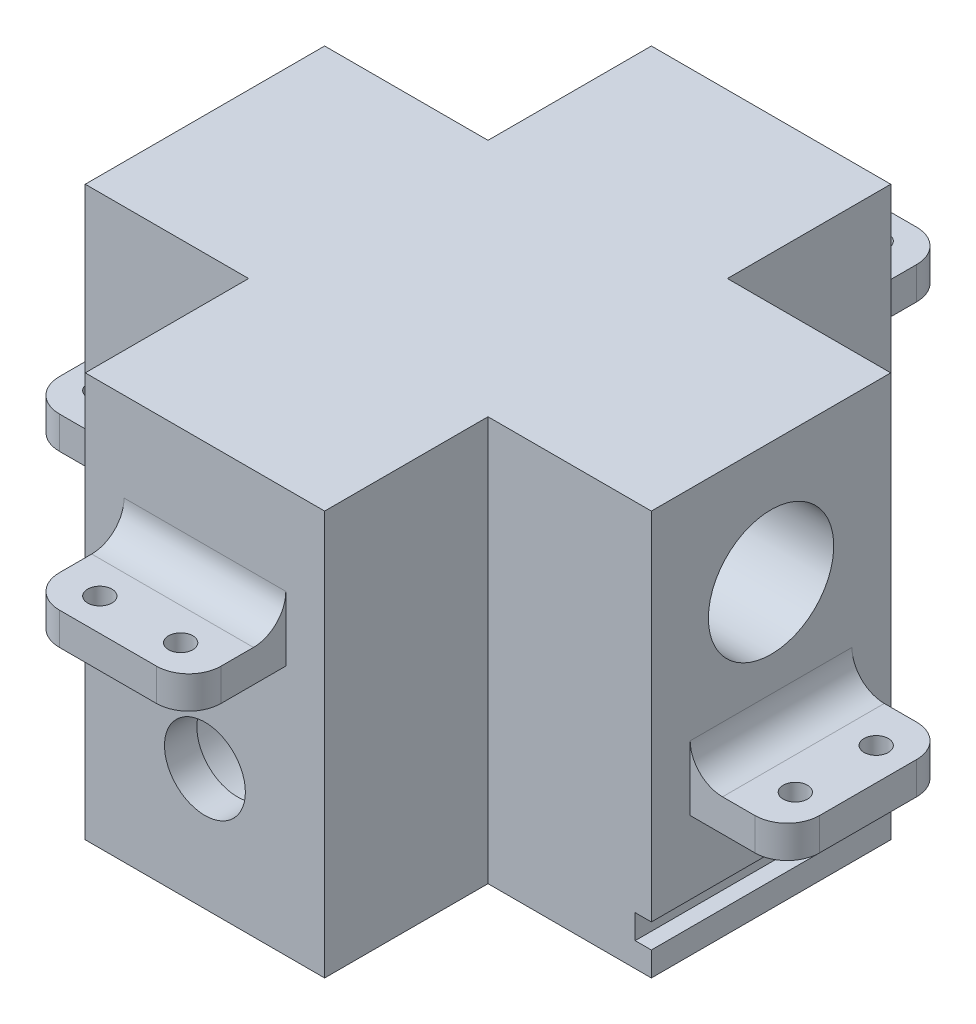
SolidWorks part; units mm, degrees
ref_plane "Plan de face" through (0, 0, 0) normal (0, 0, 1) x (1, 0, 0)
ref_plane "Plan de dessus" through (0, 0, 0) normal (0, 1, 0) x (1, 0, 0)
ref_plane "Plan de droite" through (0, 0, 0) normal (1, 0, 0) x (0, 0, -1)
sketch "Esquisse1" plane through (0, 0, 0) normal (1, 0, 0) x (0, 0, -1)
  line L2 (0, 0) -> (70, 0)
  line L3 (0, 0) -> (0, 50)
  line L4 (0, 50) -> (70, 50)
  line L5 (70, 0) -> (70, 50)
  dimension "D1" = 50
  dimension "D2" = 70
extrude "Boss.-Extru.1" add sketch "Esquisse1" along normal blind 70
sketch "Esquisse2" plane through (0, 0, 0) normal (0, 0, 1) x (1, 0, 0)
  line L0 (70, 0) -> (0, 0) construction
  line L1 (0, 50) -> (0, 0) construction
  circle A0 centre (35, 15) radius 7.75
  dimension "D1" = 15.5
  dimension "D2" = 15
  dimension "D3" = 35
extrude "Enlèv. mat.-Extru.1" cut sketch "Esquisse2" against normal through all
sketch "Esquisse3" plane through (0, 0, 0) normal (-1, 0, 0) x (0, 0, 1)
  line L0 (-70, 50) -> (0, 50) construction
  line L1 (0, 50) -> (0, 0) construction
  circle A0 centre (-35, 35) radius 7.75
  dimension "D1" = 15.5
  dimension "D2" = 15
  dimension "D3" = 35
extrude "Enlèv. mat.-Extru.2" cut sketch "Esquisse3" against normal through all
sketch "Esquisse4" plane through (0, 0, 0) normal (0, -1, 0) x (1, 0, 0)
  line L1 (0, -70) -> (20.2, -70)
  line L2 (0, -70) -> (0, -49.8)
  line L3 (0, -49.8) -> (20.2, -49.8)
  line L4 (20.2, -70) -> (20.2, -49.8)
  line L5 (0, 0) -> (20.2, 0)
  line L6 (0, 0) -> (0, -20.2)
  line L7 (0, -20.2) -> (20.2, -20.2)
  line L8 (20.2, 0) -> (20.2, -20.2)
  line L9 (70, 0) -> (49.8, 0)
  line L10 (70, 0) -> (70, -20.2)
  line L11 (70, -20.2) -> (49.8, -20.2)
  line L12 (49.8, 0) -> (49.8, -20.2)
  line L13 (70, -70) -> (49.8, -70)
  line L14 (70, -70) -> (70, -49.8)
  line L15 (70, -49.8) -> (49.8, -49.8)
  line L16 (49.8, -70) -> (49.8, -49.8)
  dimension "D1" = 20.2
  dimension "D2" = 20.2
  dimension "D3" = 20.2
  dimension "D4" = 20.2
  dimension "D5" = 20.2
  dimension "D6" = 20.2
  dimension "D7" = 20.2
  dimension "D8" = 20.2
extrude "Enlèv. mat.-Extru.3" cut sketch "Esquisse4" against normal through all
sketch "Esquisse7" plane through (0, 0, 0) normal (0, 0, 1) x (1, 0, 0)
  circle A0 centre (35, 15) radius 5
  circle A1 centre (35, 15) radius 11.7367
  dimension "D1" = 10
extrude "Boss.-Extru.3" add sketch "Esquisse7" against normal blind 4
sketch "Esquisse8" plane through (0, 0, 0) normal (-1, 0, 0) x (0, 0, 1)
  circle A0 centre (-35, 35) radius 12.1967
  circle A1 centre (-35, 35) radius 5
  dimension "D1" = 10
extrude "Boss.-Extru.4" add sketch "Esquisse8" against normal blind 4
sketch "Esquisse9" plane through (20.2, 0, 0) normal (-1, 0, 0) x (0, 0, 1)
  line L0 (-70, 50) -> (-70, 0) construction
  line L1 (-70, 6) -> (-68, 6)
  line L2 (-70, 6) -> (-70, 3)
  line L3 (-70, 3) -> (-68, 3)
  line L4 (-68, 6) -> (-68, 3)
  line L5 (-70, 0) -> (-49.8, 0) construction
  dimension "D1" = 3
  dimension "D2" = 3
  dimension "D3" = 2
extrude "Enlèv. mat.-Extru.4" cut sketch "Esquisse9" against normal through all
sketch "Esquisse10" plane through (0, 0, -49.8) normal (0, 0, -1) x (-1, 0, 0)
  line L0 (0, 50) -> (0, 0) construction
  line L1 (0, 3) -> (-2, 3)
  line L2 (0, 3) -> (0, 6)
  line L3 (0, 6) -> (-2, 6)
  line L4 (-2, 3) -> (-2, 6)
  line L5 (-20.2, 0) -> (0, 0) construction
  dimension "D1" = 3
  dimension "D2" = 2
  dimension "D3" = 3
extrude "Enlèv. mat.-Extru.5" cut sketch "Esquisse10" against normal through all
sketch "Esquisse11" plane through (0, 0, -49.8) normal (0, 0, -1) x (-1, 0, 0)
  line L0 (-70, 50) -> (-70, 0) construction
  line L1 (-70, 6) -> (-68, 6)
  line L2 (-70, 6) -> (-70, 3)
  line L3 (-70, 3) -> (-68, 3)
  line L4 (-68, 6) -> (-68, 3)
  line L5 (-70, 0) -> (-49.8, 0) construction
  dimension "D1" = 3
  dimension "D2" = 3
  dimension "D3" = 2
extrude "Enlèv. mat.-Extru.6" cut sketch "Esquisse11" against normal through all
sketch "Esquisse12" plane through (0, 0, 0) normal (-1, 0, 0) x (0, 0, 1)
  line L0 (-49.8, 50) -> (-49.8, 6) construction
  line L1 (-25, 15) -> (-45, 15)
  line L2 (-25, 15) -> (-25, 19)
  line L3 (-25, 19) -> (-45, 19)
  line L4 (-45, 15) -> (-45, 19)
  line L5 (-20.2, 50) -> (-20.2, 6) construction
  line L6 (-20.2, 0) -> (-49.8, 0) construction
  dimension "D1" = 4
  dimension "D2" = 20
  dimension "D3" = 4.8
  dimension "D4" = 4.8
  dimension "D5" = 15
extrude "Boss.-Extru.5" add sketch "Esquisse12" along normal blind 12
sketch "Esquisse13" plane through (0, 15, 0) normal (0, -1, 0) x (1, 0, 0)
  line L0 (0, -45) -> (0, -25) construction
  line L1 (-12, -45) -> (0, -45) construction
  line L2 (-12, -25) -> (0, -25) construction
  circle A0 centre (-8, -30) radius 1.5
  circle A1 centre (-8, -40) radius 1.5
  dimension "D1" = 3
  dimension "D2" = 3
  dimension "D3" = 8
  dimension "D4" = 8
  dimension "D5" = 10
  dimension "D6" = 5
  dimension "D7" = 5
extrude "Enlèv. mat.-Extru.7" cut sketch "Esquisse13" against normal through all
fillet "Congé1" radius 4 2 edges at (-12, 17, -25) (-12, 17, -45)
sketch "Esquisse14" plane through (70, 0, 0) normal (1, 0, 0) x (0, 0, -1)
  line L0 (49.8, 50) -> (49.8, 6) construction
  line L1 (45, 15) -> (25, 15)
  line L2 (45, 15) -> (45, 19)
  line L3 (45, 19) -> (25, 19)
  line L4 (25, 15) -> (25, 19)
  line L5 (20.2, 50) -> (20.2, 6) construction
  line L6 (20.2, 0) -> (49.8, 0) construction
  dimension "D1" = 4
  dimension "D2" = 20
  dimension "D3" = 4.8
  dimension "D4" = 4.8
  dimension "D5" = 15
extrude "Boss.-Extru.6" add sketch "Esquisse14" along normal blind 12
sketch "Esquisse15" plane through (0, 15, 0) normal (0, -1, 0) x (1, 0, 0)
  line L0 (82, -45) -> (70, -45) construction
  line L1 (70, -25) -> (70, -45) construction
  line L2 (82, -25) -> (70, -25) construction
  circle A0 centre (78, -40) radius 1.5
  circle A1 centre (78, -30) radius 1.5
  dimension "D1" = 3
  dimension "D2" = 3
  dimension "D3" = 10
  dimension "D4" = 5
  dimension "D5" = 8
  dimension "D6" = 5
extrude "Enlèv. mat.-Extru.8" cut sketch "Esquisse15" against normal through all
fillet "Congé3" radius 4 2 edges at (82, 17, -45) (82, 17, -25)
sketch "Esquisse16" plane through (0, 0, 0) normal (0, 0, 1) x (1, 0, 0)
  line L0 (49.8, 50) -> (20.2, 50) construction
  line L1 (45, 31) -> (25, 31)
  line L2 (45, 31) -> (45, 35)
  line L3 (45, 35) -> (25, 35)
  line L4 (25, 31) -> (25, 35)
  line L5 (20.2, 50) -> (20.2, 0) construction
  line L6 (49.8, 50) -> (49.8, 0) construction
  dimension "D1" = 20
  dimension "D2" = 4
  dimension "D3" = 15
  dimension "D4" = 4.8
  dimension "D5" = 4.8
extrude "Boss.-Extru.7" add sketch "Esquisse16" along normal blind 12
sketch "Esquisse17" plane through (0, 31, 0) normal (0, -1, 0) x (1, 0, 0)
  line L0 (25, 0) -> (45, 0) construction
  line L1 (25, 12) -> (25, 0) construction
  circle A0 centre (40, 8) radius 1.5
  circle A1 centre (30, 8) radius 1.5
  dimension "D1" = 3
  dimension "D2" = 3
  dimension "D3" = 10
  dimension "D4" = 8
  dimension "D5" = 8
  dimension "D6" = 5
extrude "Enlèv. mat.-Extru.9" cut sketch "Esquisse17" against normal through all
fillet "Congé4" radius 4 2 edges at (45, 33, 12) (25, 33, 12)
sketch "Esquisse18" plane through (0, 0, -70) normal (0, 0, -1) x (-1, 0, 0)
  line L0 (-49.8, 50) -> (-20.2, 50) construction
  line L1 (-25, 31) -> (-45, 31)
  line L2 (-25, 31) -> (-25, 35)
  line L3 (-25, 35) -> (-45, 35)
  line L4 (-45, 31) -> (-45, 35)
  line L5 (-20.2, 50) -> (-20.2, 6) construction
  line L6 (-49.8, 50) -> (-49.8, 6) construction
  point P4 (-35, 50)
  dimension "D1" = 4
  dimension "D2" = 20
  dimension "D3" = 15
  dimension "D4" = 4.8
  dimension "D5" = 4.8
extrude "Boss.-Extru.8" add sketch "Esquisse18" along normal blind 12
sketch "Esquisse19" plane through (0, 31, 0) normal (0, -1, 0) x (1, 0, 0)
  line L0 (45, -70) -> (25, -70) construction
  line L1 (25, -82) -> (25, -70) construction
  line L2 (45, -82) -> (45, -70) construction
  circle A0 centre (30, -78) radius 1.5
  circle A1 centre (40, -78) radius 1.5
  dimension "D1" = 3
  dimension "D2" = 3
  dimension "D3" = 10
  dimension "D4" = 8
  dimension "D5" = 8
  dimension "D6" = 5
  dimension "D7" = 5
extrude "Enlèv. mat.-Extru.10" cut sketch "Esquisse19" against normal through all
fillet "Congé5" radius 4 2 edges at (45, 33, -82) (25, 33, -82)
fillet "Congé6" radius 4 4 edges at (70, 19, -35) (35, 35, 0) (0, 19, -35) (35, 35, -70)
